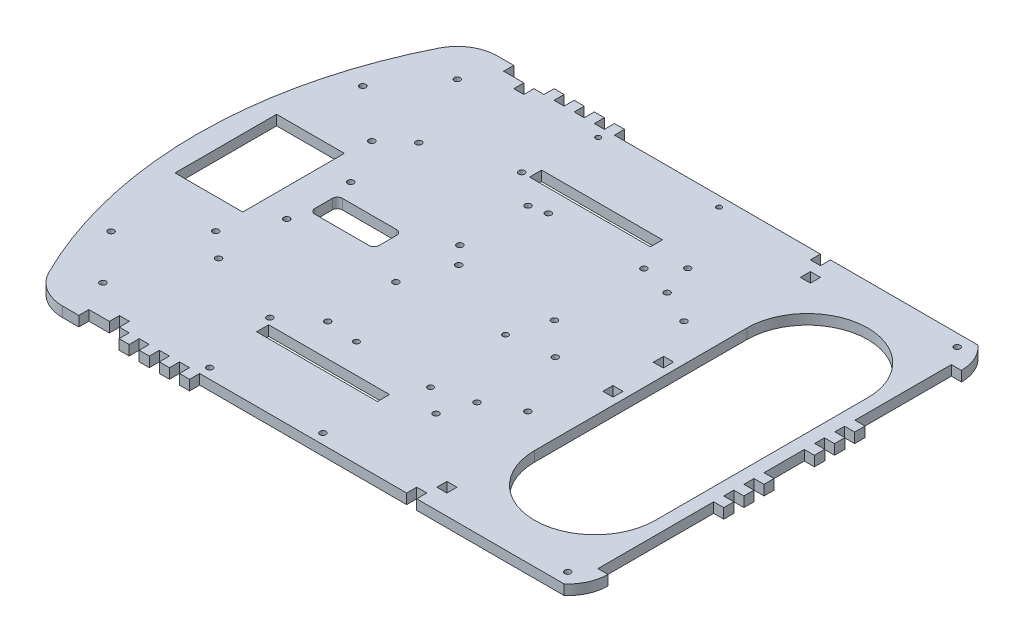
SolidWorks part; units mm, degrees
ref_plane "Front Plane" through (0, 0, 0) normal (0, 0, 1) x (1, 0, 0)
ref_plane "Top Plane" through (0, 0, 0) normal (0, 1, 0) x (1, 0, 0)
ref_plane "Right Plane" through (0, 0, 0) normal (1, 0, 0) x (0, 0, -1)
sketch "main_base_sketch" plane through (0, 0, 0) normal (0, 1, 0) x (1, 0, 0)
  line L1 (111.125, 92.7285) -> (111.125, 23.3533) construction
  line L2 (111.125, -38.1761) -> (111.125, 0) construction
  line L3 (111.125, -99.4864) -> (111.125, -136.4602) construction
  line L4 (-143.0563, 19.2252) -> (-143.0563, 29.3852)
  line L5 (111.125, 23.3533) -> (111.125, 0) construction
  line L7 (111.125, 92.7285) -> (111.125, 23.3533) construction
  line L9 (111.125, 0) -> (111.125, 23.3533) construction
  line L10 (111.125, 0) -> (111.125, -38.1761) construction
  line L11 (111.125, 0) -> (111.125, -38.1761) construction
  line L20 (-111.125, 0) -> (111.125, 0) construction
  line L24 (-94.9614, 130.8285) -> (-94.9614, 124.4785) construction
  line L25 (-94.9614, 124.4785) -> (-82.2614, 124.4785)
  line L27 (-95.6016, -142.8102) -> (111.125, -142.8102) construction
  line L28 (-95.6016, -142.8102) -> (-95.6016, -136.4602)
  line L29 (-95.6016, -136.4602) -> (-82.6643, -136.4602)
  line L32 (-94.9614, 130.8285) -> (-63.2114, 130.8285) construction
  line L34 (111.125, -136.4602) -> (111.125, -142.8102) construction
  line L36 (111.125, -136.4602) -> (111.125, -142.8102) construction
  line L38 (111.125, 12.7) -> (117.4276, 12.7)
  line L43 (-25.7516, -142.8102) -> (-0.3516, -142.8102) construction
  line L44 (-25.7516, -142.8102) -> (-25.7516, -92.0102) construction
  line L52 (111.125, 12.7) -> (111.125, 19.2555)
  line L53 (111.125, 23.3533) -> (111.125, 0) construction
  line L54 (111.125, 19.2555) -> (117.4276, 19.2555)
  line L55 (-94.9614, 130.8285) -> (-63.2114, 130.8285) construction
  line L58 (111.125, 118.1285) -> (111.125, 92.7285) construction
  line L61 (-95.6016, -142.8102) -> (111.125, -142.8102) construction
  line L62 (111.125, -99.4864) -> (111.125, -136.4602) construction
  line L64 (111.125, 118.1285) -> (111.125, 92.7285) construction
  line L66 (212.725, 105.4285) -> (212.725, -117.4102) construction
  line L67 (117.4276, 12.7) -> (117.4276, 19.2555)
  line L68 (111.125, -12.7) -> (117.475, -12.7)
  line L69 (111.125, -12.7) -> (111.125, -19.05)
  line L70 (111.125, -19.05) -> (117.475, -19.05)
  line L71 (117.475, -12.7) -> (117.475, -19.05)
  line L72 (111.125, 105.4285) -> (117.475, 105.4285)
  line L73 (111.125, 105.4285) -> (111.125, 111.7785)
  line L74 (111.125, 111.7785) -> (117.475, 111.7785)
  line L75 (117.475, 105.4285) -> (117.475, 111.7785)
  line L76 (111.125, -117.4102) -> (117.475, -117.4102)
  line L77 (111.125, -117.4102) -> (111.125, -123.7602)
  line L78 (111.125, -123.7602) -> (117.475, -123.7602)
  line L79 (117.475, -117.4102) -> (117.475, -123.7602)
  line L80 (212.725, 105.4285) -> (206.375, 105.4285)
  line L81 (212.725, 105.4285) -> (212.725, -117.4102) construction
  line L82 (212.725, -117.4102) -> (206.375, -117.4102)
  line L84 (-69.5614, 130.8285) -> (-63.2114, 130.8285)
  line L85 (-69.5614, 130.8285) -> (-69.5614, 124.4785)
  line L86 (-69.5614, 124.4785) -> (-63.2114, 124.4785) construction
  line L87 (-63.2114, 130.8285) -> (-63.2114, 124.4785)
  line L99 (-69.5614, 124.4785) -> (-63.2114, 124.4785) construction
  line L106 (-25.1114, 124.4785) -> (104.775, 124.4785)
  line L123 (113.5668, 124.4785) -> (204.1255, 124.4785)
  line L124 (206.375, 105.4285) -> (206.375, 44.6555)
  line L127 (113.5668, 124.4785) -> (111.125, 124.4785)
  line L128 (111.125, 124.4785) -> (111.125, 118.1285)
  line L130 (111.125, -136.4602) -> (204.1255, -136.4602)
  line L136 (161.925, 130.8285) -> (187.325, 130.8285) construction
  line L138 (161.925, 130.8285) -> (187.325, 130.8285) construction
  line L139 (-63.2114, 124.4785) -> (-56.8614, 124.4785)
  line L140 (-56.8614, 130.8285) -> (-50.5114, 130.8285)
  line L141 (111.125, 130.8285) -> (111.125, 124.4785) construction
  line L142 (111.125, 130.8285) -> (111.125, 124.4785) construction
  line L151 (206.375, -12.7) -> (212.725, -12.7)
  line L152 (206.375, -12.7) -> (206.375, -19.05) construction
  line L153 (206.375, -19.05) -> (212.725, -19.05)
  line L154 (212.725, -12.7) -> (212.725, -19.05)
  line L155 (206.375, -12.7) -> (206.375, -19.05) construction
  line L156 (206.375, -19.05) -> (206.375, -25.4)
  line L157 (206.375, 19.2555) -> (212.725, 19.2555)
  line L158 (212.725, 19.2555) -> (212.725, 12.7)
  line L159 (212.725, 12.7) -> (206.375, 12.7)
  line L160 (206.375, 24.1792) -> (206.375, 19.2555)
  line L161 (206.375, 12.7) -> (206.375, -12.7)
  line L162 (-70.2016, -136.4602) -> (-70.2016, -142.8102)
  line L163 (-70.2016, -142.8102) -> (-63.8516, -142.8102)
  line L164 (-63.8516, -142.8102) -> (-63.8516, -136.4602)
  line L165 (-70.2016, -136.4602) -> (-63.8516, -136.4602) construction
  line L166 (-63.8516, -136.4602) -> (-57.5016, -136.4602)
  line L167 (-57.5016, -142.8102) -> (-51.1516, -142.8102)
  line L168 (-57.5016, -136.4602) -> (-57.5016, -142.8102)
  line L169 (-51.1516, -142.8102) -> (-51.1516, -136.4602)
  line L170 (-44.8016, -142.8102) -> (-38.4516, -142.8102)
  line L171 (-44.8016, -136.4602) -> (-44.8016, -142.8102)
  line L172 (-38.4516, -142.8102) -> (-38.4516, -136.4602)
  line L173 (-32.1016, -142.8102) -> (-25.7516, -142.8102)
  line L174 (-32.1016, -136.4602) -> (-32.1016, -142.8102)
  line L175 (-25.7516, -142.8102) -> (-25.7516, -136.4602)
  line L176 (-57.5016, -136.4602) -> (-51.1516, -136.4602) construction
  line L177 (-51.1516, -136.4602) -> (-44.8016, -136.4602)
  line L178 (-44.8016, -136.4602) -> (-38.4516, -136.4602) construction
  line L179 (-38.4516, -136.4602) -> (-32.1016, -136.4602)
  line L180 (-32.1016, -136.4602) -> (-25.7516, -136.4602) construction
  line L181 (-25.7516, -136.4602) -> (104.775, -136.4602)
  line L202 (212.725, 25.4) -> (206.375, 25.4)
  line L203 (212.725, 31.9555) -> (212.725, 25.4)
  line L204 (206.375, 31.9555) -> (212.725, 31.9555)
  line L205 (212.725, 38.1) -> (206.375, 38.1)
  line L206 (212.725, 44.6555) -> (212.725, 38.1)
  line L207 (206.375, 44.6555) -> (212.725, 44.6555)
  line L208 (206.375, 31.9555) -> (206.375, 25.4) construction
  line L209 (206.375, 25.4) -> (206.375, 24.1792)
  line L210 (206.375, 44.6555) -> (206.375, 38.1) construction
  line L211 (206.375, 38.1) -> (206.375, 31.9555)
  line L212 (206.375, -31.75) -> (212.725, -31.75)
  line L213 (212.725, -25.4) -> (212.725, -31.75)
  line L214 (206.375, -25.4) -> (212.725, -25.4)
  line L215 (206.375, -44.45) -> (212.725, -44.45)
  line L216 (212.725, -38.1) -> (212.725, -44.45)
  line L217 (206.375, -38.1) -> (212.725, -38.1)
  line L218 (206.375, -25.4) -> (206.375, -31.75) construction
  line L219 (206.375, -31.75) -> (206.375, -38.1)
  line L220 (206.375, -38.1) -> (206.375, -44.45) construction
  line L221 (206.375, -44.45) -> (206.375, -117.4102)
  line L225 (-95.5505, 130.8285) -> (-157.7358, 130.8285) construction
  line L229 (-132.8963, 29.3852) -> (-110.4973, 29.3852)
  line L230 (-143.0563, 19.2252) -> (-143.0563, -24.5291)
  line L231 (-132.8963, -34.6891) -> (-110.4973, -34.6891)
  line L238 (-100.3373, 19.2252) -> (-100.3373, -24.5291)
  line L248 (-94.9614, 130.8285) -> (-95.5505, 130.8285) construction
  line L254 (-94.9614, 130.8285) -> (-95.5505, 130.8285) construction
  line L257 (-94.9614, 130.8285) -> (-105.2412, 130.8285)
  line L258 (-95.5505, 130.8285) -> (-94.9614, 130.8285) construction
  line L259 (-95.6016, -142.8102) -> (-105.7982, -142.8102)
  line L260 (-94.9614, 124.4785) -> (-94.9614, 130.8285)
  line L261 (-94.9614, 130.8285) -> (-95.5505, 130.8285) construction
  line L262 (-82.2614, 124.4785) -> (-75.9114, 124.4785) construction
  line L263 (-82.2614, 124.4785) -> (-75.9114, 124.4785) construction
  line L264 (-82.2614, 124.4785) -> (-82.2614, 118.1285)
  line L265 (-82.2614, 118.1285) -> (-75.9114, 118.1285)
  line L266 (-75.9114, 124.4785) -> (-75.9114, 118.1285)
  line L267 (-97.1554, -142.8102) -> (-95.6016, -142.8102) construction
  line L269 (-75.9114, 124.4785) -> (-69.5614, 124.4785)
  line L270 (104.775, 124.4785) -> (111.125, 124.4785) construction
  line L271 (111.125, 124.4785) -> (104.775, 124.4785) construction
  line L274 (111.125, 118.1285) -> (104.775, 118.1285)
  line L280 (104.775, 124.4785) -> (104.775, 118.1285)
  line L282 (104.775, -136.4602) -> (111.125, -136.4602) construction
  line L285 (111.125, -136.4602) -> (104.775, -136.4602) construction
  line L286 (111.125, -136.4602) -> (111.125, -130.1018)
  line L289 (111.125, -130.1018) -> (104.775, -130.1018)
  line L291 (104.775, -136.4602) -> (104.775, -130.1018)
  line L293 (-82.6643, -136.4602) -> (-76.4089, -136.4602) construction
  line L294 (-94.9614, 130.8285) -> (-95.5505, 130.8285) construction
  line L295 (-157.7358, 130.8285) -> (-157.7358, -142.8102) construction
  line L296 (-157.7358, -142.8102) -> (-97.1554, -142.8102) construction
  line L297 (-95.5505, 130.8285) -> (-157.7358, 130.8285) construction
  line L298 (-82.6643, -136.4602) -> (-76.4089, -136.4602) construction
  line L299 (-82.6643, -136.4602) -> (-82.6643, -130.1018)
  line L300 (-82.6643, -130.1018) -> (-76.4089, -130.1018)
  line L301 (-76.4089, -136.4602) -> (-76.4089, -130.1018)
  line L302 (-76.4089, -136.4602) -> (-70.2016, -136.4602)
  line L303 (-25.7516, -92.0102) -> (-0.3516, -92.0102) construction
  line L304 (-0.3516, -142.8102) -> (-0.3516, -92.0102) construction
  line L305 (-25.1114, 124.4785) -> (0, 124.4785) construction
  line L306 (-29.0195, 124.4785) -> (-29.0195, 78.7585) construction
  line L307 (-29.0195, 78.7585) -> (0, 78.7585) construction
  line L308 (0, 124.4785) -> (0, 78.7585) construction
  line L309 (-29.0195, 82.4735) -> (47.1805, 82.4735)
  line L310 (-29.0195, 82.4735) -> (-29.0195, 74.8535)
  line L311 (-29.0195, 74.8535) -> (47.1805, 74.8535)
  line L312 (47.1805, 82.4735) -> (47.1805, 74.8535)
  line L313 (-30.5765, -88.0878) -> (45.6235, -88.0878)
  line L314 (-30.5765, -88.0878) -> (-30.5765, -95.7078)
  line L315 (-30.5765, -95.7078) -> (45.6235, -95.7078)
  line L316 (45.6235, -88.0878) -> (45.6235, -95.7078)
  line L317 (-143.0563, 29.3852) -> (-132.8963, 29.3852)
  line L318 (-110.4973, 29.3852) -> (-100.3373, 29.3852)
  line L319 (-100.3373, 29.3852) -> (-100.3373, 19.2252)
  line L320 (-100.3373, -24.5291) -> (-100.3373, -34.6891)
  line L321 (-100.3373, -34.6891) -> (-110.4973, -34.6891)
  line L322 (-132.8963, -34.6891) -> (-143.0563, -34.6891)
  line L323 (-143.0563, -34.6891) -> (-143.0563, -24.5291)
  line L324 (121.92, 60.9785) -> (121.92, -72.9602)
  line L325 (198.12, -72.9602) -> (198.12, 60.9785)
  line L326 (-50.5114, 130.8285) -> (-50.5114, 124.4785)
  line L327 (-56.8614, 130.8285) -> (-56.8614, 124.4785)
  line L328 (-44.1614, 130.8285) -> (-37.8114, 130.8285)
  line L329 (-37.8114, 130.8285) -> (-37.8114, 124.4785)
  line L330 (-44.1614, 130.8285) -> (-44.1614, 124.4785)
  line L331 (-31.4614, 130.8285) -> (-25.1114, 130.8285)
  line L332 (-25.1114, 130.8285) -> (-25.1114, 124.4785)
  line L333 (-31.4614, 130.8285) -> (-31.4614, 124.4785)
  line L334 (-50.5114, 124.4785) -> (-44.1614, 124.4785)
  line L335 (-37.8114, 124.4785) -> (-31.4614, 124.4785)
  arc A34 (212.725, -117.4102) -> (204.1255, -136.4602) centre (187.325, -117.4102) cw
  arc A35 (212.725, 105.4285) -> (204.1255, 124.4785) centre (187.325, 105.4285) ccw
  arc A37 (198.12, 60.9785) -> (121.92, 60.9785) centre (160.02, 60.9785) ccw
  arc A38 (121.92, -72.9602) -> (198.12, -72.9602) centre (160.02, -72.9602) ccw
  arc A41 (-127.9188, 116.8691) -> (-128.5327, -128.7374) centre (116.7138, -6.5464) ccw
  arc A42 (-127.9188, 116.8691) -> (-105.2412, 130.8285) centre (-105.2412, 105.4285) cw
  arc A43 (-128.5327, -128.7374) -> (-105.7982, -142.8102) centre (-105.7982, -117.4102) ccw
  circle A44 centre (-131.2964, 71.9636) radius 1.905
  circle A45 centre (-131.2964, -86.7864) radius 1.905
  circle A46 centre (198.6177, 116.8691) radius 1.905
  circle A47 centre (198.6177, -128.7374) radius 1.905
  circle A50 centre (-105.2412, 105.4285) radius 1.905
  circle A55 centre (-105.7982, -117.4102) radius 1.905
  circle A56 centre (-29.0195, 118.1285) radius 1.5875
  circle A58 centre (47.1805, 118.1285) radius 1.5875
  circle A59 centre (-25.7516, -130.1018) radius 1.905
  circle A60 centre (45.6235, -130.1018) radius 1.905
  point P16 (-120.3614, 130.8285)
  point P19 (212.725, -142.8102)
  point P46 (-121.0016, -142.8102)
  point P123 (0, 0)
  dimension "D7" = 63.5
  dimension "D12" = 25.4
  dimension "D13" = 25.4
  dimension "D21" = 63.5
  dimension "D24" = 76.2
  dimension "D26" = 76.2
  dimension "D14" = 25.4
  dimension "D30" = 3.81
  dimension "D31" = 6.35
  dimension "D4" = 76.2
  dimension "D9" = 6.35
  dimension "D23" = 76.2
  dimension "D25" = 6.35
  dimension "D34" = 3.175
  dimension "D35" = 3.175
  dimension "D37" = 4
  dimension "D11" = 4
  dimension "D15" = 25.4
  dimension "D16" = 50.8
  dimension "D17" = 45.72
  dimension "D18" = 7.62
  dimension "D19" = 6.35
  dimension "D22" = 7.62
  dimension "D27" = 10.2799
  dimension "D28" = 10.1966
  dimension "D29" = 6.5555
  dimension "D32" = 6.35
  dimension "D33" = 6.35
  dimension "D36" = 6.35
  dimension "D57" = 38.1
  dimension "D58" = 6.35
  dimension "D59" = 101.6
  dimension "D60" = 6.3026
  dimension "D61" = 12.7
  dimension "D62" = 12.7
  dimension "D63" = 6.35
  dimension "D64" = 6.35
  dimension "D65" = 6.35
  dimension "D66" = 6.35
  dimension "D67" = 12.7
  dimension "D68" = 12.7
  dimension "D69" = 6.35
  dimension "D70" = 6.35
  dimension "D72" = 6.35
  dimension "D74" = 6.35
  dimension "D76" = 3
  dimension "D77" = 3
  dimension "D78" = 6.3585
extrude "main_base" add sketch "main_base_sketch" along normal blind 6.35
sketch "Sketch1" plane through (0, 6.35, 0) normal (0, 1, 0) x (1, 0, 0)
  line L20 (-111.125, -4.4655) -> (111.125, -4.4655) construction
  line L39 (-42.259, -13.1472) -> (-76.4089, -13.1472)
  line L40 (-39.084, -9.9722) -> (-39.084, 1.0411)
  line L41 (-42.259, 4.2161) -> (-76.4089, 4.2161)
  line L42 (-79.5839, -9.9722) -> (-79.5839, 1.0411)
  line L43 (-39.084, -13.1472) -> (-79.5839, 4.2161) construction
  line L44 (-39.084, 4.2161) -> (-79.5839, -13.1472) construction
  line L45 (61.595, 59.0345) -> (93.345, 59.0345) construction
  line L46 (61.595, 59.0345) -> (61.595, -67.9655) construction
  line L47 (61.595, -67.9655) -> (93.345, -67.9655) construction
  line L48 (93.345, 59.0345) -> (93.345, -67.9655) construction
  line L49 (61.595, 59.0345) -> (93.345, -67.9655) construction
  line L50 (61.595, -67.9655) -> (93.345, 59.0345) construction
  circle A0 centre (-82.6643, 58.6916) radius 1.905
  circle A1 centre (-13.8303, 58.6916) radius 1.905
  arc A2 (-76.4089, -13.1472) -> (-79.5839, -9.9722) centre (-76.4089, -9.9722) cw
  arc A3 (-42.259, -13.1472) -> (-39.084, -9.9722) centre (-42.259, -9.9722) ccw
  arc A4 (-39.084, 1.0411) -> (-42.259, 4.2161) centre (-42.259, 1.0411) ccw
  arc A5 (-76.4089, 4.2161) -> (-79.5839, 1.0411) centre (-76.4089, 1.0411) ccw
  circle A10 centre (-3.2843, 60.9395) radius 1.905
  circle A11 centre (-13.8303, 15.6894) radius 1.905
  circle A12 centre (-3.2843, 4.4753) radius 1.905
  circle A13 centre (-82.6643, 15.6894) radius 1.905
  circle A14 centre (-82.6643, -24.6204) radius 1.905
  circle A15 centre (-13.8303, -24.6204) radius 1.905
  circle A16 centre (-82.6643, -67.6226) radius 1.905
  circle A17 centre (-13.8303, -67.6226) radius 1.905
  circle A18 centre (6.29, -69.6017) radius 1.796
  circle A19 centre (54.55, -71.1892) radius 1.796
  circle A20 centre (49.47, -18.8017) radius 1.796
  circle A21 centre (57.0407, 4.4753) radius 1.905
  circle A22 centre (57.0407, 60.9395) radius 1.905
  circle A23 centre (-98.425, 44.7683) radius 1.905
  circle A24 centre (-34.0871, 74.9095) radius 1.905
  circle A25 centre (70.6863, 74.9095) radius 1.905
  circle A26 centre (98.425, 44.7683) radius 1.905
  circle A27 centre (98.425, -53.6993) radius 1.905
  circle A28 centre (70.6863, -83.8405) radius 1.905
  circle A29 centre (-34.0871, -83.8405) radius 1.905
  circle A30 centre (-98.425, -53.6993) radius 1.905
  circle A31 centre (77.47, -64.7905) radius 1.905
  circle A32 centre (77.47, 55.0657) radius 1.905
  circle A33 centre (77.47, -15.4193) radius 1.905
  point P40 (-59.334, -4.4655)
  point P111 (77.47, -67.9655)
  point P113 (77.47, -4.4655)
  dimension "D1" = 3.175
  dimension "D40" = 3.81
  dimension "D41" = 3.81
  dimension "D42" = 3.81
  dimension "D43" = 3.592
  dimension "D44" = 3.592
  dimension "D45" = 3.592
  dimension "D9" = 40.4999
  dimension "D10" = 17.3633
  dimension "D15" = 104.7734
  dimension "D24" = 60.325
  dimension "D33" = 68.834
  dimension "D35" = 20.1549
  dimension "D36" = 20.1549
  dimension "D37" = 35.7997
  dimension "D46" = 1.5875
  dimension "D47" = 48.26
  dimension "D48" = 127
  dimension "D49" = 31.75
  dimension "D51" = 3.175
  dimension "D52" = 3.9688
  dimension "D53" = 70.485
  dimension "D54" = 56.4642
  dimension "D55" = 23.277
  dimension "D56" = 74.077
extrude "Cut-Extrude1" cut sketch "Sketch1" against normal through all
